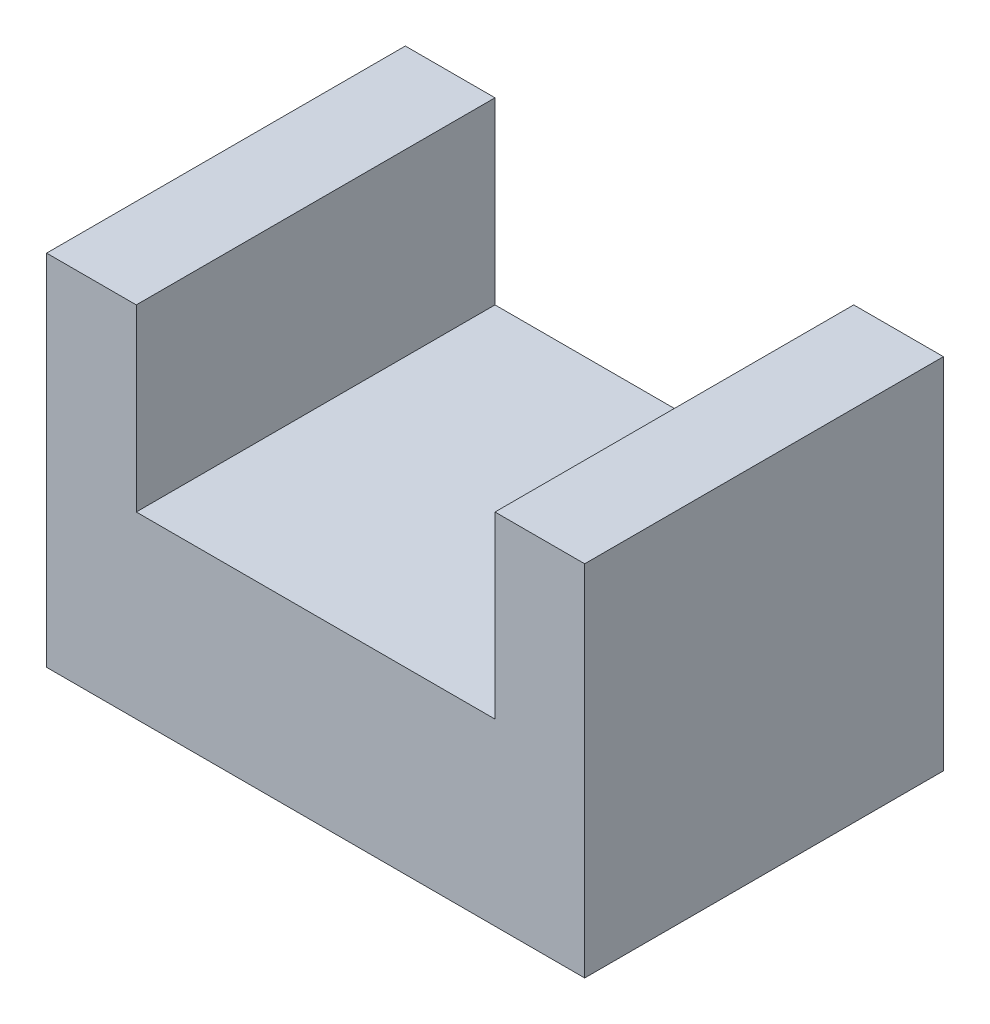
SolidWorks part; units mm, degrees
ref_plane "Front" through (0, 0, 0) normal (0, 0, 1) x (1, 0, 0)
ref_plane "Top" through (0, 0, 0) normal (0, 1, 0) x (1, 0, 0)
ref_plane "Right" through (0, 0, 0) normal (1, 0, 0) x (0, 0, -1)
sketch "Sketch1" plane through (0, 0, 0) normal (0, 0, 1) x (1, 0, 0)
  line L0 (-43.5237, 33.9383) -> (-43.5237, -16.8617)
  line L1 (-43.5237, -16.8617) -> (32.6763, -16.8617)
  line L2 (32.6763, -16.8617) -> (32.6763, 33.9383)
  line L3 (32.6763, 33.9383) -> (19.9763, 33.9383)
  line L4 (19.9763, 33.9383) -> (19.9763, 8.5383)
  line L5 (19.9763, 8.5383) -> (-30.8237, 8.5383)
  line L6 (-30.8237, 8.5383) -> (-30.8237, 33.9383)
  line L7 (-30.8237, 33.9383) -> (-43.5237, 33.9383)
  dimension "D1" = 76.2
  dimension "D2" = 50.8
  dimension "D3" = 12.7
  dimension "D4" = 25.4
  dimension "D5" = 50.8
  dimension "D7" = 12.7
extrude "Boss-Extrude1" add sketch "Sketch1" along normal blind 50.8
